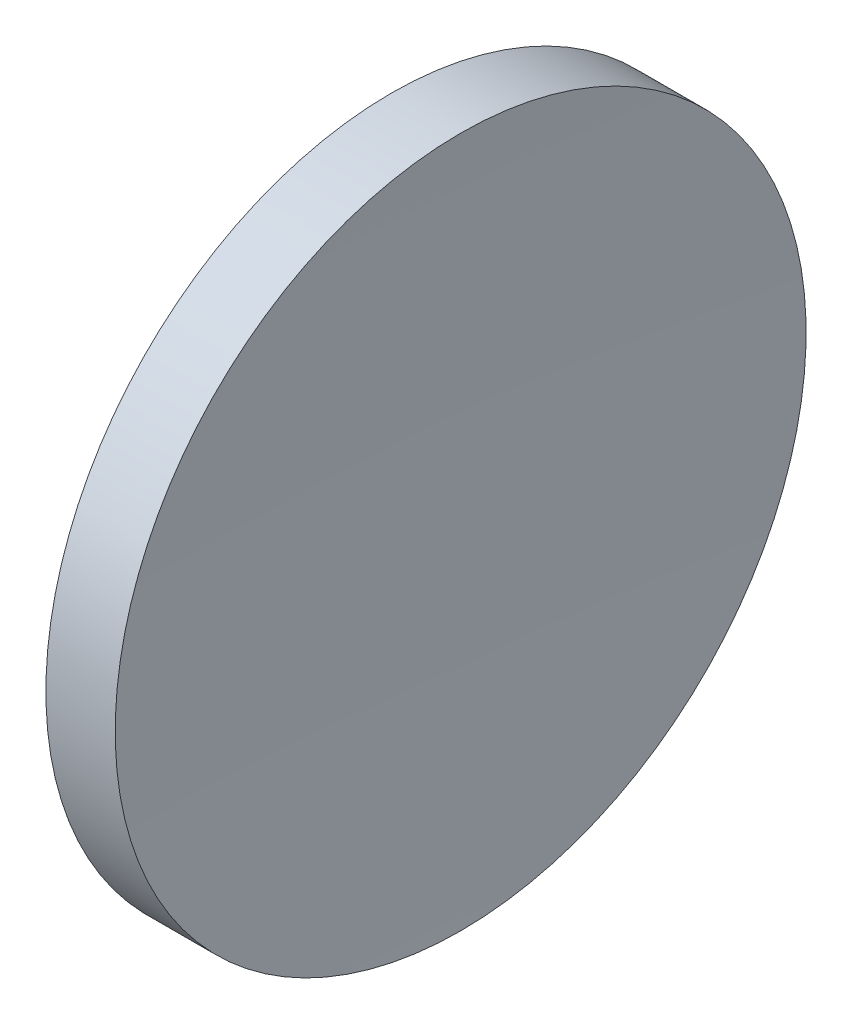
SolidWorks part; units mm, degrees
ref_plane "前视基准面" through (0, 0, 0) normal (0, 0, 1) x (1, 0, 0)
ref_plane "上视基准面" through (0, 0, 0) normal (0, 1, 0) x (1, 0, 0)
ref_plane "右视基准面" through (0, 0, 0) normal (1, 0, 0) x (0, 0, -1)
sketch "草图1" plane through (0, 0, 0) normal (0, 0, 1) x (1, 0, 0)
  line L0 (89.8587, 52.1781) -> (104.0854, 52.1781) construction
  line L1 (97.0904, 52.1781) -> (95.0904, 52.1781)
  line L3 (96.0904, 64.8781) -> (97.3648, 64.8781)
  line L4 (96.0904, 64.8781) -> (94.8161, 64.8781)
  arc A0 (95.0904, 52.1781) -> (94.8161, 64.8781) centre (-186.0094, 52.4587) ccw
  arc A1 (97.3648, 64.8781) -> (97.0904, 52.1781) centre (378.1903, 52.4587) ccw
revolve "旋转1" add sketch "草图1" angle 360 about L0
